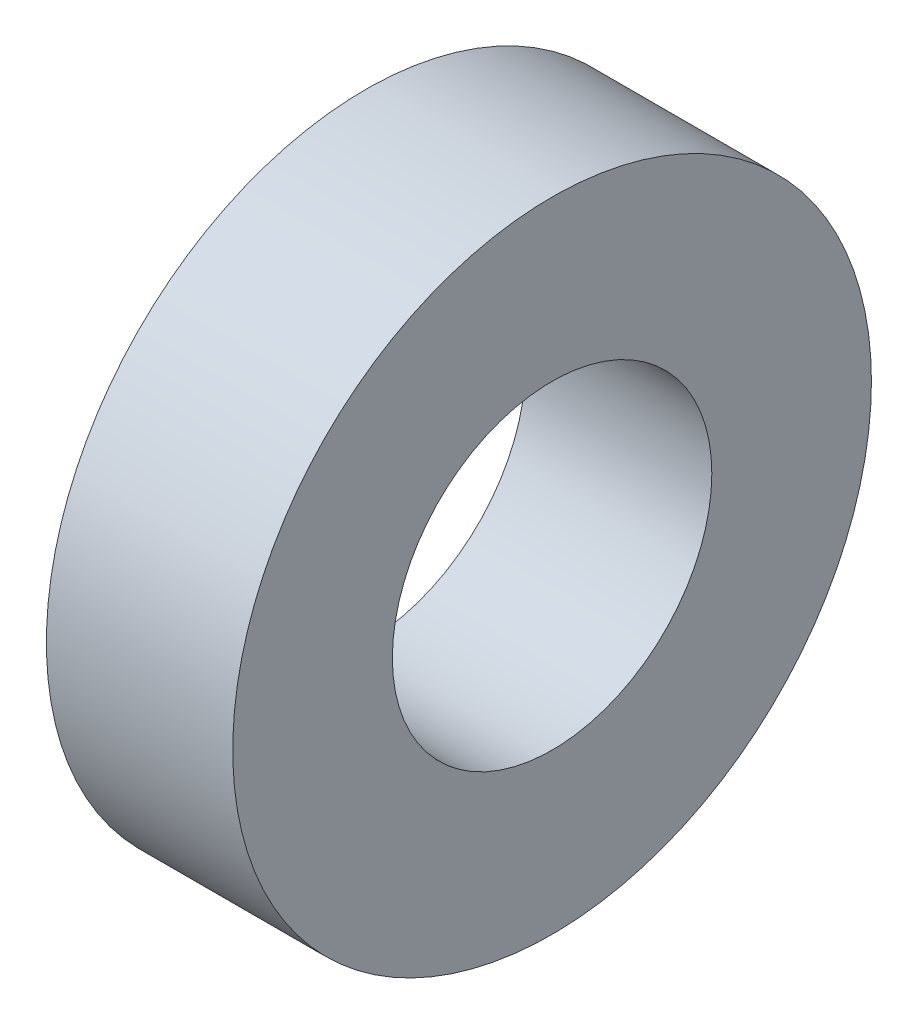
SolidWorks part; units mm, degrees
ref_plane "Front Plane" through (0, 0, 0) normal (0, 0, 1) x (1, 0, 0)
ref_plane "Top Plane" through (0, 0, 0) normal (0, 1, 0) x (1, 0, 0)
ref_plane "Right Plane" through (0, 0, 0) normal (1, 0, 0) x (0, 0, -1)
sketch "Sketch1" plane through (0, 0, 0) normal (1, 0, 0) x (0, 0, -1)
  circle A0 centre (0, 0) radius 30
  circle A1 centre (0, 0) radius 59.9781
extrude "Boss-Extrude2" add sketch "Sketch1" along normal blind 35
